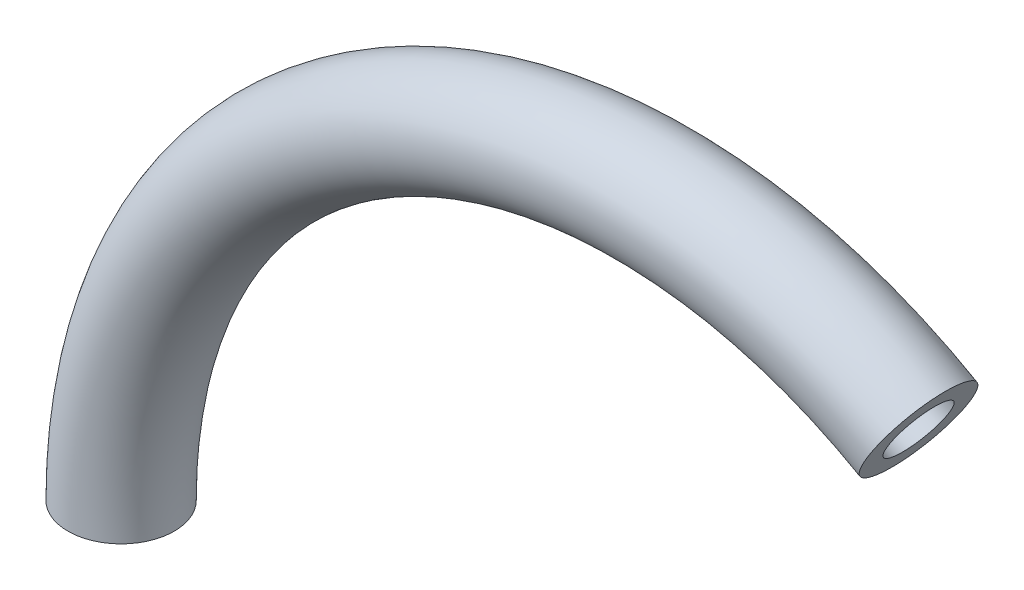
SolidWorks part; units mm, degrees
ref_plane "Front Plane" through (0, 0, 0) normal (0, 0, 1) x (1, 0, 0)
ref_plane "Top Plane" through (0, 0, 0) normal (0, 1, 0) x (1, 0, 0)
ref_plane "Right Plane" through (0, 0, 0) normal (1, 0, 0) x (0, 0, -1)
sketch "Sketch1" plane through (0, 0, 0) normal (0, 1, 0) x (1, 0, 0)
  circle A0 centre (-63.5, 0) radius 6.35
  point P2 (0, 0)
  dimension "D1" = 12.7
  dimension "D2" = 63.5
sketch "Sketch2" plane through (0, 0, 0) normal (0, 0, 1) x (1, 0, 0)
  line L0 (-57.15, 0) -> (-69.85, 0) construction
  line L1 (0, 0) -> (-63.5, 0) construction
  line L2 (0, 0) -> (31.75, 54.9926) construction
  arc A0 (-63.5, 0) -> (31.75, 54.9926) centre (0, 0) cw
  dimension "D1" = 120
sweep "Sweep1" add profiles "Sketch1" path "Sketch2"
shell "Shell1" thickness 2.54
